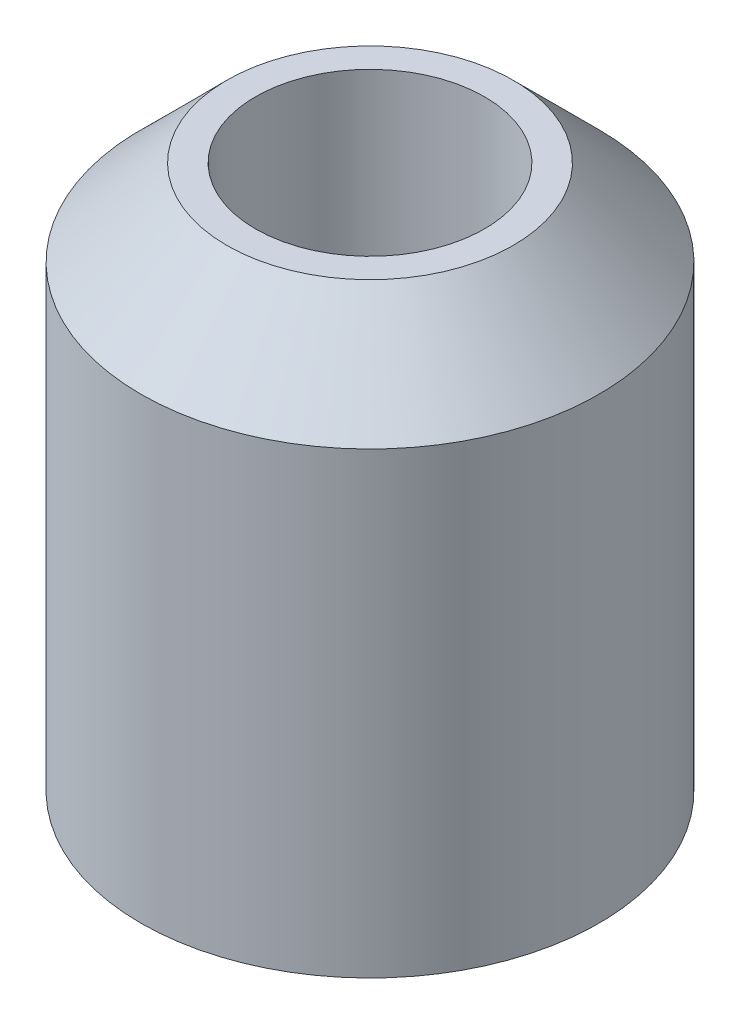
SolidWorks part; units mm, degrees
material "2014-T6"
ref_plane "Ebene vorne" through (0, 0, 0) normal (0, 0, 1) x (1, 0, 0)
ref_plane "Ebene oben" through (0, 0, 0) normal (0, 1, 0) x (1, 0, 0)
ref_plane "Ebene rechts" through (0, 0, 0) normal (1, 0, 0) x (0, 0, -1)
sketch "Skizze1" plane through (0, 0, 0) normal (0, 0, 1) x (1, 0, 0)
  line L0 (0, 27.213) -> (0, -17.3174) construction
  line L1 (-2, 9.5) -> (-2.5, 9.5)
  line L2 (-2.5, 9.5) -> (-4, 8)
  line L3 (-4, 8) -> (-4, 0)
  line L4 (-4, 0) -> (-2, 0)
  line L5 (-2, 0) -> (-2, 9.5)
  line L6 (-2, 0) -> (0, 0) construction
  dimension "D1" = 4
  dimension "D2" = 8
  dimension "D3" = 9.5
  dimension "D4" = 5
  dimension "D5" = 45
revolve "Rotation1" add sketch "Skizze1" angle 360 about L0
